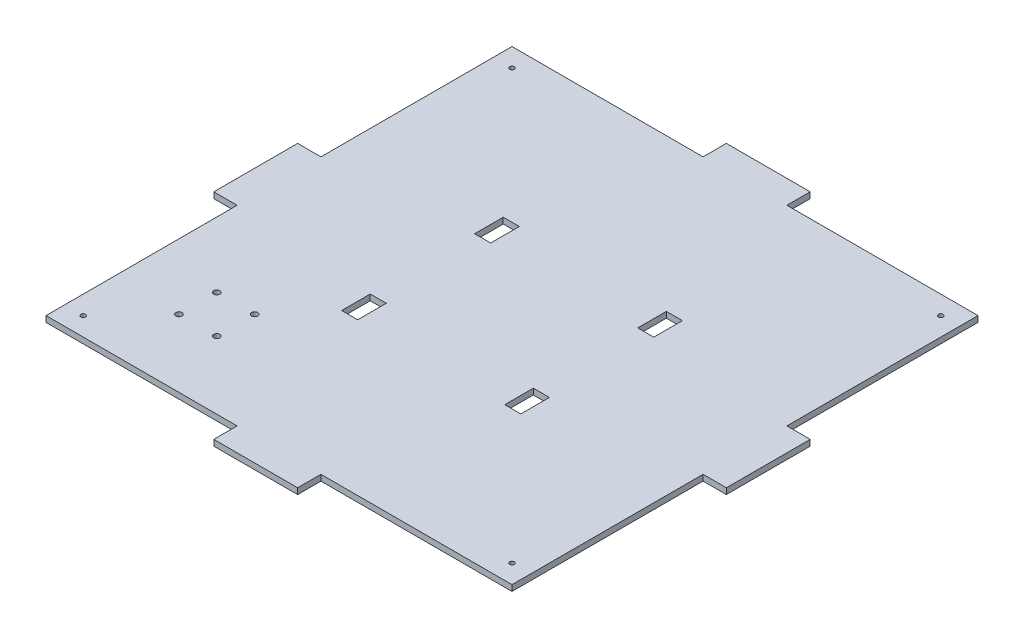
SolidWorks part; units mm, degrees
ref_plane "Front Plane" through (0, 0, 0) normal (0, 0, 1) x (1, 0, 0)
ref_plane "Top Plane" through (0, 0, 0) normal (0, 1, 0) x (1, 0, 0)
ref_plane "Right Plane" through (0, 0, 0) normal (1, 0, 0) x (0, 0, -1)
sketch "Sketch2" plane through (0, 0, 0) normal (0, 1, 0) x (1, 0, 0)
  line L1 (-125, -125) -> (125, -125)
  line L2 (-125, -125) -> (-125, 125)
  line L3 (-125, 125) -> (125, 125)
  line L4 (125, -125) -> (125, 125)
  line L5 (-125, -125) -> (125, 125) construction
  line L6 (-125, 125) -> (125, -125) construction
  point P0 (0, 0)
  dimension "D1" = 250
  dimension "250" = 250
extrude "Boss-Extrude1" add sketch "Sketch2" along normal blind 3.175
sketch "Sketch3" plane through (0, 3.175, 0) normal (0, 1, 0) x (1, 0, 0)
  line L0 (-125, 0) -> (125, 0) construction
  line L1 (-125, 125) -> (-125, -125) construction
  line L2 (125, -125) -> (125, 125) construction
  line L3 (-43.75, 125) -> (-43.75, -125) construction
  line L4 (125, 125) -> (-125, 125) construction
  line L5 (-125, -125) -> (125, -125) construction
  line L6 (0, 125) -> (0, -125) construction
  line L11 (-48.05, 28) -> (-39.45, 28)
  line L12 (-48.05, 28) -> (-48.05, 43.35)
  line L13 (-48.05, 43.35) -> (-39.45, 43.35)
  line L14 (-39.45, 28) -> (-39.45, 43.35)
  line L15 (-48.05, 28) -> (-39.45, 43.35) construction
  line L16 (-48.05, 43.35) -> (-39.45, 28) construction
  line L21 (-48.05, -43.35) -> (-39.45, -43.35)
  line L22 (-48.05, -43.35) -> (-48.05, -28)
  line L23 (-48.05, -28) -> (-39.45, -28)
  line L24 (-39.45, -43.35) -> (-39.45, -28)
  line L25 (-48.05, -43.35) -> (-39.45, -28) construction
  line L26 (-48.05, -28) -> (-39.45, -43.35) construction
  line L27 (48.05, -28) -> (39.45, -28)
  line L28 (39.45, -43.35) -> (39.45, -28)
  line L29 (48.05, -43.35) -> (39.45, -43.35)
  line L30 (48.05, -43.35) -> (48.05, -28)
  line L31 (48.05, 43.35) -> (39.45, 43.35)
  line L32 (39.45, 28) -> (39.45, 43.35)
  line L33 (48.05, 28) -> (39.45, 28)
  line L34 (48.05, 28) -> (48.05, 43.35)
  point P12 (-43.75, 35.675)
  point P17 (-43.75, -35.675)
  dimension "D1" = 43.75
  dimension "D2" = 8.6
  dimension "D3" = 15.35
  dimension "D4" = 56
  dimension "D5" = 28
extrude "Cut-Extrude1" cut sketch "Sketch3" against normal blind 10
sketch "Sketch10" plane through (0, 0, -125) normal (0, 0, -1) x (-1, 0, 0)
  line L0 (-125, 1.5875) -> (125, 1.5875) construction
  line L1 (-125, 3.175) -> (-125, 0) construction
  line L2 (125, 3.175) -> (125, 0) construction
  line L8 (-125, 3.175) -> (125, 3.175) construction
  line L9 (-22.5, 0) -> (22.5, 0)
  line L10 (-22.5, 0) -> (-22.5, 3.175)
  line L11 (-22.5, 3.175) -> (22.5, 3.175)
  line L12 (22.5, 0) -> (22.5, 3.175)
  line L13 (-22.5, 0) -> (22.5, 3.175) construction
  line L14 (-22.5, 3.175) -> (22.5, 0) construction
  point P6 (0, 1.5875)
  dimension "D1" = 45
extrude "Boss-Extrude2" add sketch "Sketch10" along normal blind 12.5
sketch "Sketch11" plane through (-125, 0, 0) normal (-1, 0, 0) x (0, 0, 1)
  line L0 (-125, 1.5875) -> (125, 1.5875) construction
  line L1 (-125, 3.175) -> (-125, 0) construction
  line L2 (125, 3.175) -> (125, 0) construction
  line L9 (-22.5, 0) -> (22.5, 0)
  line L10 (-22.5, 0) -> (-22.5, 3.175)
  line L11 (-22.5, 3.175) -> (22.5, 3.175)
  line L12 (22.5, 0) -> (22.5, 3.175)
  line L13 (-22.5, 0) -> (22.5, 3.175) construction
  line L14 (-22.5, 3.175) -> (22.5, 0) construction
  point P6 (0, 1.5875)
  dimension "D1" = 45
  dimension "D2" = 3.175
extrude "Boss-Extrude3" add sketch "Sketch11" along normal blind 12.5
sketch "Sketch13" plane through (0, 0, 125) normal (0, 0, 1) x (1, 0, 0)
  line L0 (-125, 1.5875) -> (125, 1.5875) construction
  line L3 (-125, 0) -> (-125, 3.175) construction
  line L9 (-22.5, 0) -> (22.5, 0)
  line L10 (-22.5, 0) -> (-22.5, 3.175)
  line L11 (-22.5, 3.175) -> (22.5, 3.175)
  line L12 (22.5, 0) -> (22.5, 3.175)
  line L13 (-22.5, 0) -> (22.5, 3.175) construction
  line L14 (-22.5, 3.175) -> (22.5, 0) construction
  line L15 (125, 3.175) -> (125, 0) construction
  point P6 (0, 1.5875)
  dimension "D1" = 45
  dimension "D2" = 3.175
extrude "Boss-Extrude4" add sketch "Sketch13" along normal blind 12.5
sketch "Sketch14" plane through (125, 0, 0) normal (1, 0, 0) x (0, 0, -1)
  line L0 (-125, 1.5875) -> (125, 1.5875) construction
  line L3 (-125, 3.175) -> (-125, 0) construction
  line L9 (-22.5, 0) -> (22.5, 0)
  line L10 (-22.5, 0) -> (-22.5, 3.175)
  line L11 (-22.5, 3.175) -> (22.5, 3.175)
  line L12 (22.5, 0) -> (22.5, 3.175)
  line L13 (-22.5, 0) -> (22.5, 3.175) construction
  line L14 (-22.5, 3.175) -> (22.5, 0) construction
  line L15 (125, 3.175) -> (125, 0) construction
  point P6 (0, 1.5875)
  dimension "D1" = 45
  dimension "D2" = 3.175
extrude "Boss-Extrude5" add sketch "Sketch14" along normal blind 12.5
hole_wizard "M3 Tapped Hole1" positions "3DSketch4" profile "Sketch20" tap size "M3" standard "ISO" end condition through all
sketch3d "3DSketch4"
  line L0 (-22.5, 3.175, -125) -> (-125, 3.175, -125) construction
  line L1 (-125, 3.175, -125) -> (-125, 3.175, -22.5) construction
  point P0 (-115, 3.175, -115)
  dimension "D1" = 10
  dimension "D2" = 10
sketch "Sketch20" plane through (-115, 3.175, -115) normal (1, 0, 0) x (0, 0, 1)
  line L0 (0, 0) -> (0, 3.175)
  line L1 (0, 3.175) -> (1.25, 3.175)
  line L2 (1.25, 3.175) -> (1.25, 0)
  line L5 (1.25, 0) -> (0, 0)
  line L11 (0, -6.35) -> (0, 107.95) construction
  dimension "Thru Tap Drill Dia." = 2.5
  dimension "Thru Tap Drill Depth" = 3.175
cosmetic thread "Hole Thread1" parameters "D2"=3
sketch "Sketch21" plane through (0, 3.175, 0) normal (0, 1, 0) x (1, 0, 0)
  line L0 (0, -137.5) -> (0, 137.5)
  line L1 (22.5, -137.5) -> (-22.5, -137.5) construction
  line L2 (-22.5, 137.5) -> (22.5, 137.5) construction
  line L3 (-137.5, 0) -> (137.5, 0)
  line L4 (-137.5, -22.5) -> (-137.5, 22.5) construction
  line L5 (137.5, 22.5) -> (137.5, -22.5) construction
  circle A0 centre (-115, 115) radius 1.25
  circle A1 centre (115, 115) radius 1.25
  circle A2 centre (115, -115) radius 1.25
  circle A3 centre (-115, -115) radius 1.25
extrude "Cut-Extrude2" cut sketch "Sketch21" against normal blind 10 contours A1 | A2 | A3
sketch "Sketch22" plane through (0, 3.175, 0) normal (0, 1, 0) x (1, 0, 0)
  circle A0 centre (-89.965, -68.4042) radius 1.6519
  circle A1 centre (-69.6445, -68.4045) radius 1.6516
  circle A3 centre (-69.645, -88.7242) radius 1.6519
  circle A4 centre (-89.965, -88.7242) radius 1.651
extrude "Cut-Extrude3" cut sketch "Sketch22" against normal through all
